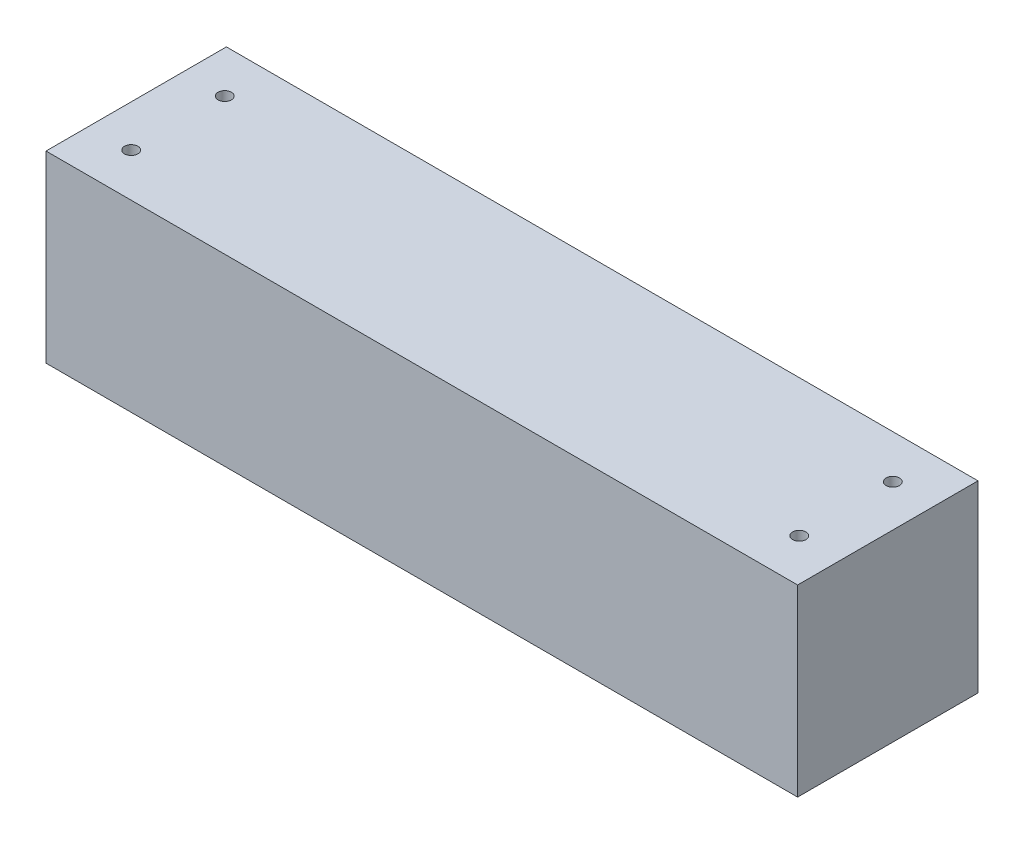
SolidWorks part; units mm, degrees
material "Acrylic (Medium-high impact)"
ref_plane "Front Plane" through (0, 0, 0) normal (0, 0, 1) x (1, 0, 0)
ref_plane "Top Plane" through (0, 0, 0) normal (0, 1, 0) x (1, 0, 0)
ref_plane "Right Plane" through (0, 0, 0) normal (1, 0, 0) x (0, 0, -1)
sketch "Sketch1" plane through (0, 0, 0) normal (0, 0, 1) x (1, 0, 0)
  line L0 (0, 0) -> (225, 0)
  line L1 (0, 0) -> (0, -55)
  line L2 (225, 0) -> (225, -55)
  line L3 (0, -55) -> (225, -55)
  dimension "D1" = 225
  dimension "D2" = 55
extrude "Boss-Extrude1" add sketch "Sketch1" along normal blind 54
shell "Shell1" thickness 4
sketch "Sketch2" plane through (0, 0, 0) normal (0, 1, 0) x (1, 0, 0)
  line L0 (112.5, 3.9839) -> (112.5, -56.0199) construction
  line L1 (-27.3279, -27) -> (252.6721, -27) construction
  line L2 (0, -4) -> (0, -50) construction
  line L3 (0, -4) -> (225, -4) construction
  line L4 (225, -54) -> (225, 0) construction
  circle A0 centre (12.5, -12.9981) radius 2
  circle A1 centre (212.5, -12.9981) radius 2
  circle A2 centre (212.5, -41.0019) radius 2
  circle A3 centre (12.5, -41.0019) radius 2
  point P14 (0, -27)
  point P17 (112.5, -4)
  dimension "D1" = 4
  dimension "D2" = 14.0019
  dimension "D3" = 100
extrude "Cut-Extrude1" cut sketch "Sketch2" against normal blind 10
